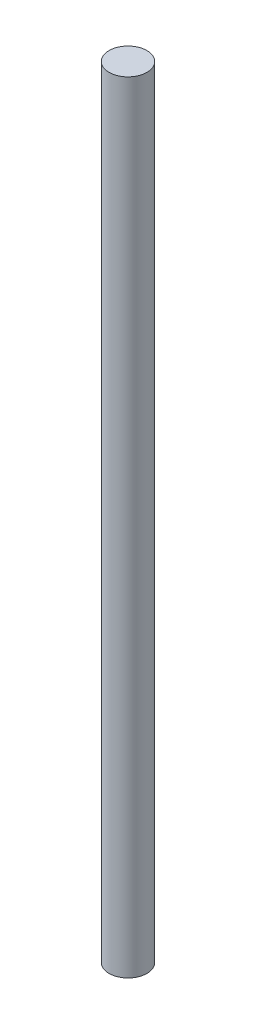
SolidWorks part; units mm, degrees
material "Balsa"
ref_plane "Front Plane" through (0, 0, 0) normal (0, 0, 1) x (1, 0, 0)
ref_plane "Top Plane" through (0, 0, 0) normal (0, 1, 0) x (1, 0, 0)
ref_plane "Right Plane" through (0, 0, 0) normal (1, 0, 0) x (0, 0, -1)
sketch "Sketch2" plane through (0, 0, 0) normal (0, 1, 0) x (1, 0, 0)
  circle A0 centre (0, 0) radius 1.6
  dimension "D1" = 3.2
extrude "Boss-Extrude1" add sketch "Sketch2" along normal blind 66
